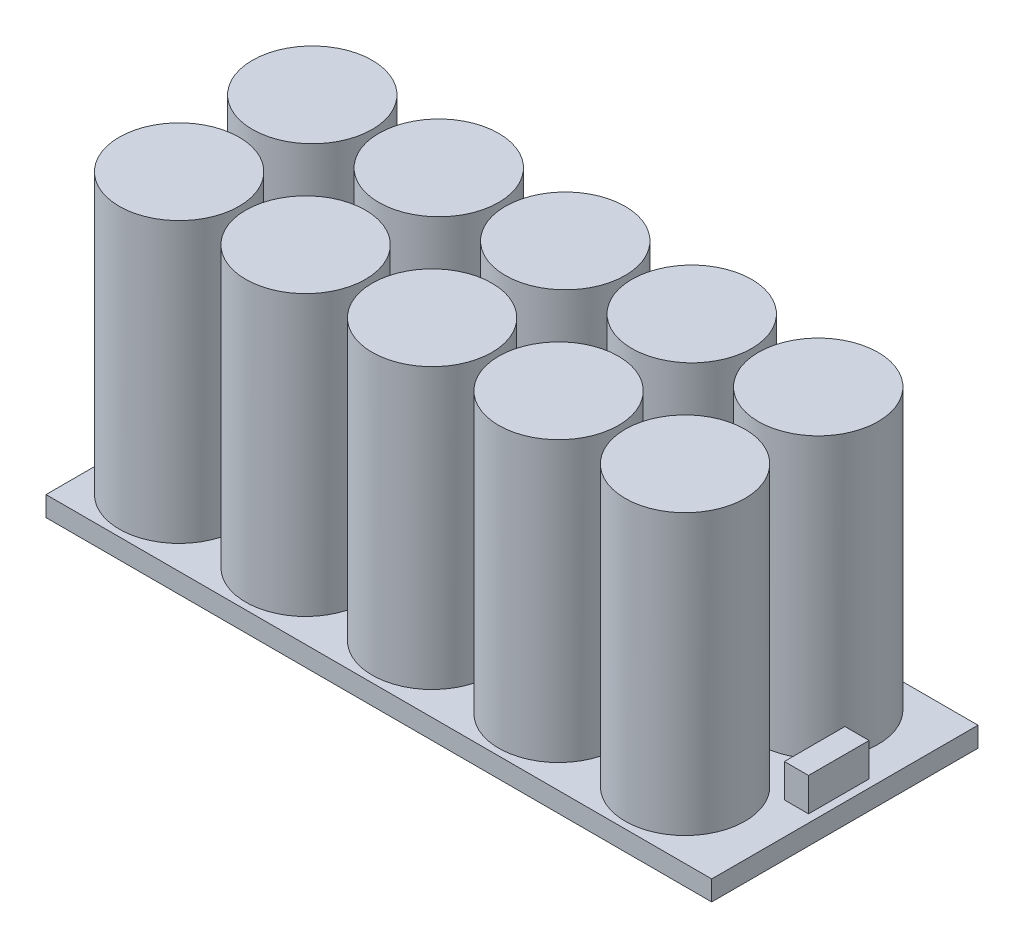
SolidWorks part; units mm, degrees
ref_plane "前视基准面" through (0, 0, 0) normal (0, 0, 1) x (1, 0, 0)
ref_plane "上视基准面" through (0, 0, 0) normal (0, 1, 0) x (1, 0, 0)
ref_plane "右视基准面" through (0, 0, 0) normal (1, 0, 0) x (0, 0, -1)
sketch "草图1" plane through (0, 0, 0) normal (0, 1, 0) x (1, 0, 0)
  line L1 (-50, -20) -> (50, -20)
  line L2 (-50, -20) -> (-50, 20)
  line L3 (-50, 20) -> (50, 20)
  line L4 (50, -20) -> (50, 20)
  line L5 (-50, -20) -> (50, 20) construction
  line L6 (-50, 20) -> (50, -20) construction
  point P0 (0, 0)
  dimension "D1" = 40
  dimension "D2" = 100
extrude "凸台-拉伸2" add sketch "草图1" along normal blind 3
sketch "草图2" plane through (0, 3, 0) normal (0, 1, 0) x (1, 0, 0)
  line L6 (-50, 20) -> (-50, -20) construction
  line L7 (-50, -20) -> (50, -20) construction
  circle A0 centre (-40, -10) radius 9
  circle A10 centre (-21, -10) radius 9
  circle A11 centre (-2, -10) radius 9
  circle A12 centre (17, -10) radius 9
  circle A13 centre (36, -10) radius 9
  circle A14 centre (-21, 10) radius 9
  circle A15 centre (-2, 10) radius 9
  circle A16 centre (17, 10) radius 9
  circle A17 centre (36, 10) radius 9
  circle A18 centre (-40, 10) radius 9
  dimension "D1" = 2
  dimension "D4" = 10
  dimension "D5" = 10
extrude "凸台-拉伸3" add sketch "草图2" along normal blind 42
sketch "草图3" plane through (0, 3, 0) normal (0, 1, 0) x (1, 0, 0)
  line L6 (45.1817, 4.8262) -> (48.8113, 4.8262)
  line L7 (45.1817, 4.8262) -> (45.1817, -4.2654)
  line L8 (45.1817, -4.2654) -> (48.8113, -4.2654)
  line L9 (48.8113, 4.8262) -> (48.8113, -4.2654)
extrude "凸台-拉伸4" add sketch "草图3" along normal blind 5
